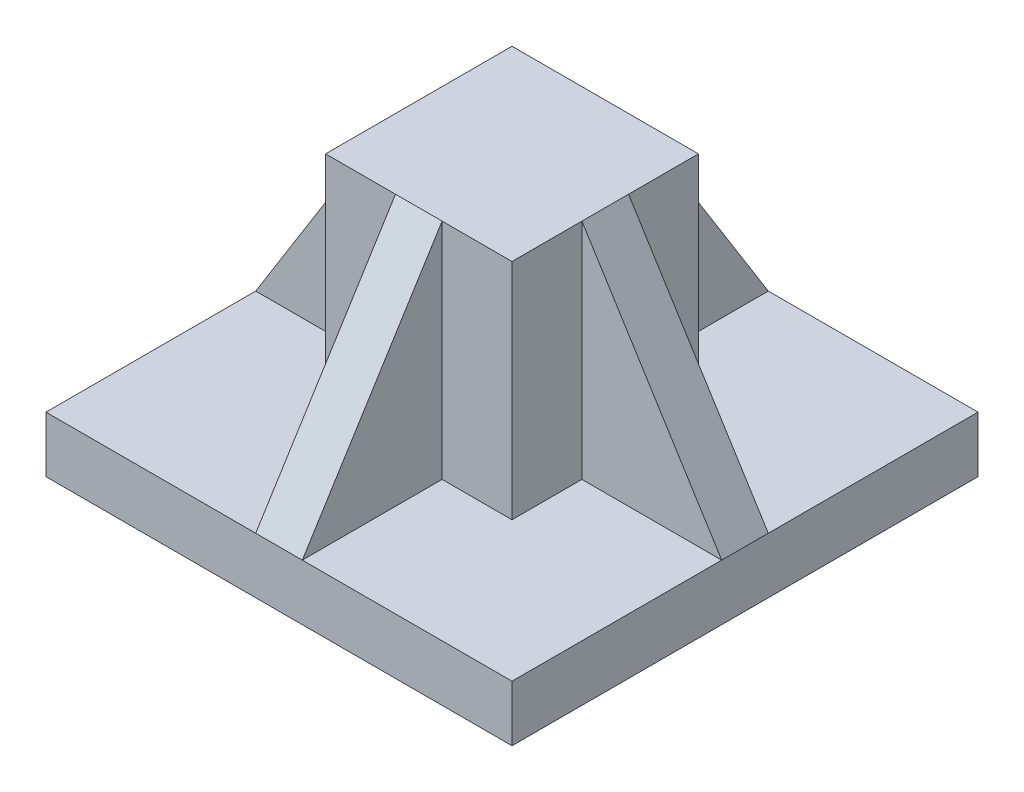
SolidWorks part; units mm, degrees
ref_plane "Alzado" through (0, 0, 0) normal (0, 0, 1) x (1, 0, 0)
ref_plane "Planta" through (0, 0, 0) normal (0, 1, 0) x (1, 0, 0)
ref_plane "Vista lateral" through (0, 0, 0) normal (1, 0, 0) x (0, 0, -1)
sketch "Croquis1" plane through (0, 0, 0) normal (0, 1, 0) x (1, 0, 0)
  line L1 (-50, -50) -> (50, -50)
  line L2 (-50, -50) -> (-50, 50)
  line L3 (-50, 50) -> (50, 50)
  line L4 (50, -50) -> (50, 50)
  line L5 (-50, -50) -> (50, 50) construction
  line L6 (-50, 50) -> (50, -50) construction
  point P0 (0, 0)
  dimension "D1" = 100
  dimension "D2" = 100
sketch "Croquis2" plane through (0, 0, 0) normal (0, 1, 0) x (1, 0, 0)
  line L1 (-20, -20) -> (20, -20)
  line L2 (-20, -20) -> (-20, 20)
  line L3 (-20, 20) -> (20, 20)
  line L4 (20, -20) -> (20, 20)
  line L5 (-20, -20) -> (20, 20) construction
  line L6 (-20, 20) -> (20, -20) construction
  point P0 (0, 0)
  dimension "D1" = 40
  dimension "D2" = 40
extrude "Saliente-Extruir1" add sketch "Croquis1" along normal blind 12
extrude "Saliente-Extruir2" add sketch "Croquis2" along normal blind 60
sketch "Croquis3" plane through (0, 0, 0) normal (0, 0, 1) x (1, 0, 0)
  line L0 (20, 60) -> (50, 12)
  line L1 (50, 12) -> (20, 12)
  line L2 (20, 12) -> (20, 60)
  line L3 (-20, 60) -> (-50, 12)
  line L4 (-20, 60) -> (-20, 12)
  line L5 (-20, 12) -> (-50, 12)
extrude "Saliente-Extruir3" add sketch "Croquis3" along normal blind 5 and the other way blind 5
sketch "Croquis4" plane through (0, 0, 0) normal (1, 0, 0) x (0, 0, -1)
  line L0 (-50, 12) -> (-20, 60)
  line L1 (-20, 60) -> (-20, 12)
  line L2 (-20, 12) -> (-50, 12)
  line L3 (20, 60) -> (50, 12)
  line L4 (50, 12) -> (20, 12)
  line L5 (20, 12) -> (20, 60)
extrude "Saliente-Extruir4" add sketch "Croquis4" along normal blind 5 and the other way blind 5
